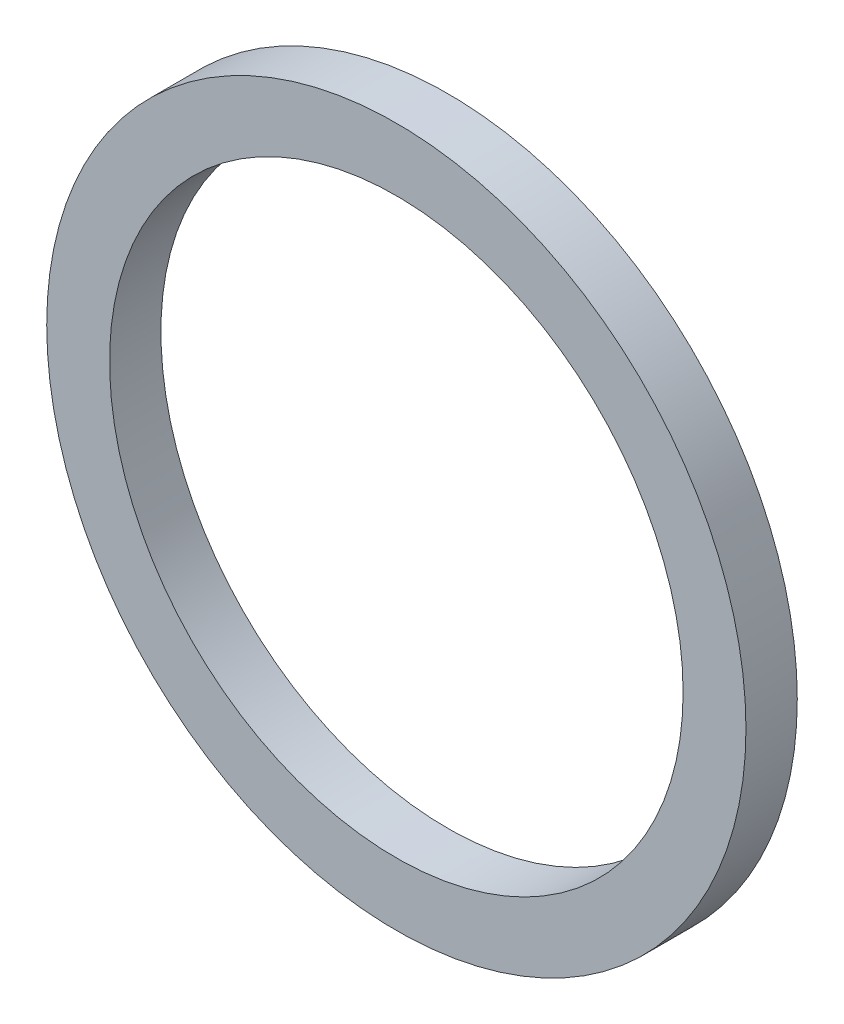
SolidWorks part; units mm, degrees
material "6061-T6 (SS)"
ref_plane "Front" through (0, 0, 0) normal (0, 0, 1) x (1, 0, 0)
ref_plane "Top" through (0, 0, 0) normal (0, 1, 0) x (1, 0, 0)
ref_plane "Right" through (0, 0, 0) normal (1, 0, 0) x (0, 0, -1)
sketch "Sketch1" plane through (0, 0, 0) normal (0, 0, 1) x (1, 0, 0)
  circle A0 centre (0, 0) radius 133.5
  circle A1 centre (0, 0) radius 109.5
extrude "Boss-Extrude1" add sketch "Sketch1" along normal blind 19.6
